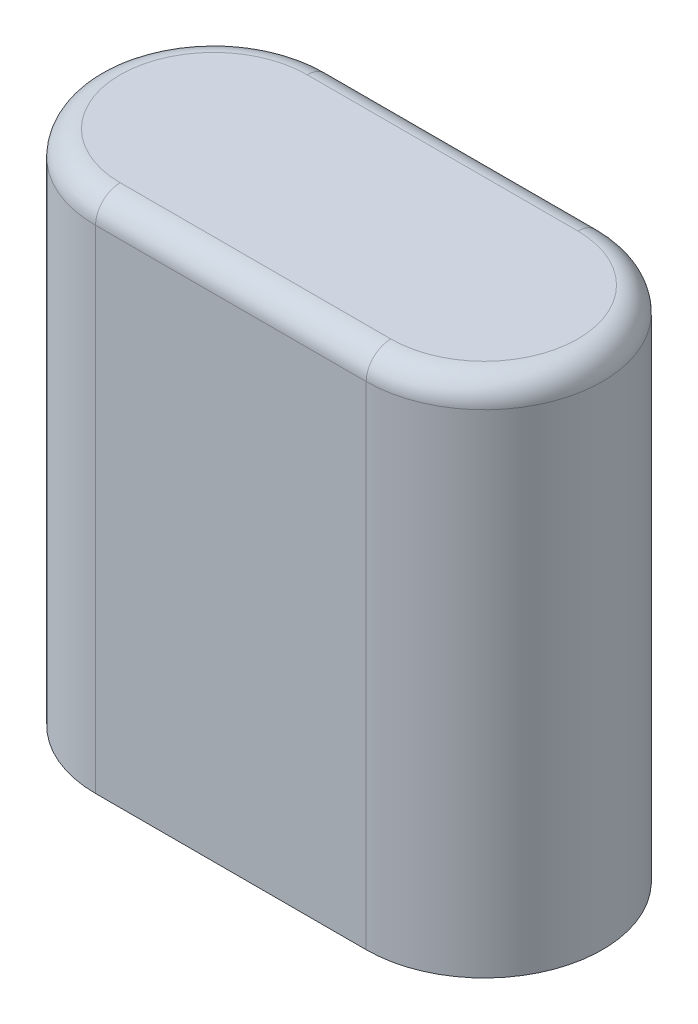
SolidWorks part; units mm, degrees
ref_plane "Front Plane" through (0, 0, 0) normal (0, 0, 1) x (1, 0, 0)
ref_plane "Top Plane" through (0, 0, 0) normal (0, 1, 0) x (1, 0, 0)
ref_plane "Right Plane" through (0, 0, 0) normal (1, 0, 0) x (0, 0, -1)
sketch "Sketch1" plane through (0, 0, 0) normal (0, 1, 0) x (1, 0, 0)
  line L0 (-3.4925, 0) -> (3.4925, 0) construction
  line L1 (-3.4925, 3.048) -> (3.4925, 3.048)
  line L2 (-3.4925, -3.048) -> (3.4925, -3.048)
  arc A0 (-3.4925, 3.048) -> (-3.4925, -3.048) centre (-3.4925, 0) ccw
  arc A1 (3.4925, -3.048) -> (3.4925, 3.048) centre (3.4925, 0) ccw
  point P2 (0, 0)
  dimension "D1" = 3.048
  dimension "D2" = 6.985
extrude "Boss-Extrude1" add sketch "Sketch1" along normal blind 13.335
fillet "Fillet1" radius 0.635 4 edges at (0, 13.335, 3.048) (-6.5405, 13.335, 0) (0, 13.335, -3.048) (6.5405, 13.335, 0)
sketch "Sketch2" plane through (0, 0, 0) normal (0, -1, 0) x (1, 0, 0)
  circle A0 centre (0, 0) radius 1.778
  dimension "D1" = 3.556
extrude "Cut-Extrude3" cut sketch "Sketch2" against normal blind 6.985
